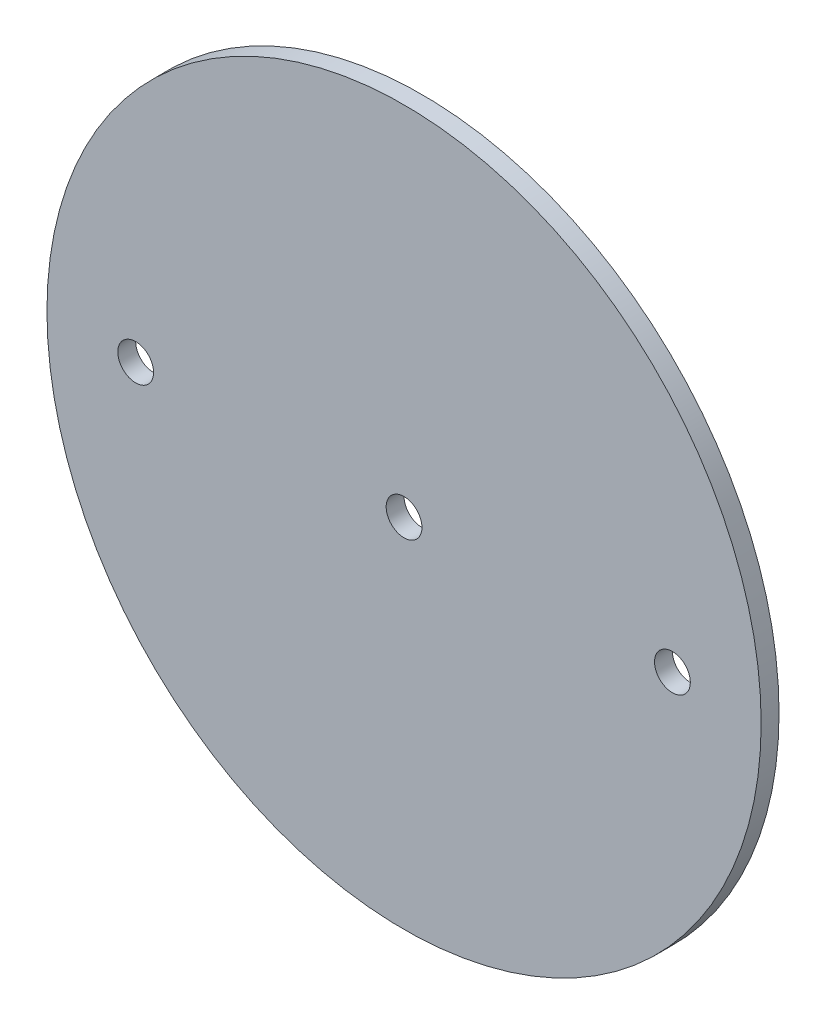
SolidWorks part; units mm, degrees
ref_plane "Front Plane" through (0, 0, 0) normal (0, 0, 1) x (1, 0, 0)
ref_plane "Top Plane" through (0, 0, 0) normal (0, 1, 0) x (1, 0, 0)
ref_plane "Right Plane" through (0, 0, 0) normal (1, 0, 0) x (0, 0, -1)
sketch "Sketch1" plane through (0, 0, 0) normal (0, 0, 1) x (1, 0, 0)
  circle A0 centre (0, 0) radius 63.373
  dimension "D1" = 126.746
extrude "Boss-Extrude1" add sketch "Sketch1" along normal mid plane 3.175
sketch "Sketch2" plane through (0, 0, 1.5875) normal (0, 0, 1) x (1, 0, 0)
  line L0 (-1000, 0) -> (49000, 0) construction
  point P1 (0, 0)
  point P4 (47.625, 0)
  point P5 (-47.625, 0)
  dimension "D1" = 47.625
  dimension "D2" = 95.25
hole_wizard "1/4 (0.25) Diameter Hole1" positions "Sketch2" profile "Sketch3" hole size "1/4" standard "ANSI Inch" end condition through all
sketch "Sketch3" plane through (-47.625, 0, 1.5875) normal (1, 0, 0) x (0, -1, 0)
  line L0 (0, 0) -> (0, 3.175)
  line L1 (0, 3.175) -> (3.175, 3.175)
  line L2 (3.175, 3.175) -> (3.175, 0)
  line L5 (3.175, 0) -> (0, 0)
  line L11 (0, -6.35) -> (0, 107.95) construction
  dimension "Thru Hole Dia." = 6.35
  dimension "Thru Hole Depth" = 3.175
equation "\"AIRFRAME_OD\"= 5.15in"
equation "\"AIRFRAME_ID\"= 4.99in"
equation "\"FLAT_T\"= 0.125in"
equation "\"NOSE_EXP_L\"= 27in"
equation "\"NOSE_SHOULDER_L\"= 5in"
equation "\"MAIN_L\"= 30in"
equation "\"RECO_COUP_L\"= 10in"
equation "\"RECO_SWITCH_L\"= 2in"
equation "\"DROGUE_L\"= 20in"
equation "\"ATS_FORE_COUP_L\"= 5.5in"
equation "\"ATS_AFT_COUP_L\"= 4.5in"
equation "\"LOWER_L\"= 30in"
equation "\"FIN_N\"= 4"
equation "\"CR_AFT_X\"= 0.5in"
equation "\"CR_FORE_X\"= 9.25in"
equation "\"FIN_ROOT\"= 8in"
equation "\"FIN_X\"= 0.75in"
equation "\"MOTOR_OD\"= 3.091in"
equation "\"MOTOR_ID\"= 3.00in"
equation "\"COUPLER_OD\"= 4.998in"
equation "\"COUPLER_ID\"= 4.85in"
equation "\"D1@Sketch1\"=\"AIRFRAME_ID\""
equation "\"D1@Boss-Extrude1\"=\"FLAT_T\""
equation "\"RECO_ROD_X\"= 3.5in"
equation "\"ATS_ROD_X\"= 3.75in"
equation "\"D1@Sketch2\"=\"ATS_ROD_X\"*0.5"
equation "\"D2@Sketch2\"=\"ATS_ROD_X\""
equation "\"MOTOR_L\"= 14in"
equation "\"MOTOR_LOWER_X\"= 2in"
